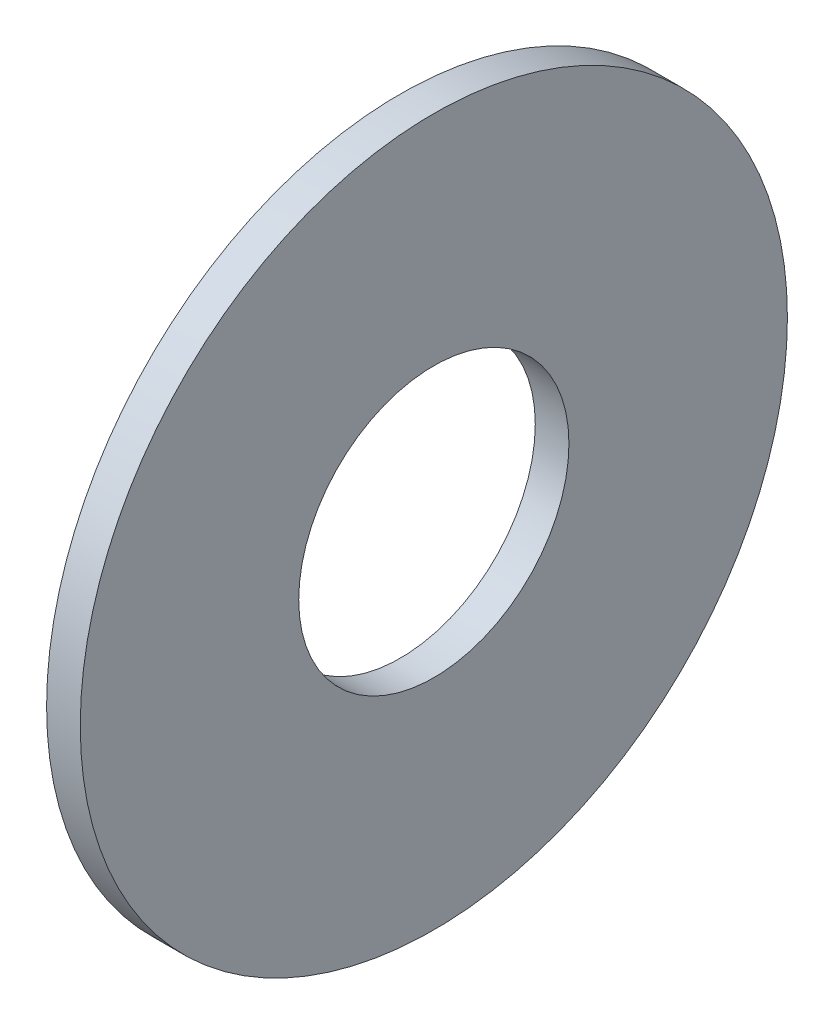
SolidWorks part; units mm, degrees
ref_plane "Front Plane" through (0, 0, 0) normal (0, 0, 1) x (1, 0, 0)
ref_plane "Top Plane" through (0, 0, 0) normal (0, 1, 0) x (1, 0, 0)
ref_plane "Right Plane" through (0, 0, 0) normal (1, 0, 0) x (0, 0, -1)
sketch "Sketch1" plane through (0, 0, 0) normal (1, 0, 0) x (0, 0, -1)
  circle A0 centre (0, 0) radius 10.5
  circle A1 centre (0, 0) radius 4 construction
  circle A2 centre (0, 0) radius 4.0125
  dimension "OD" = 21
  dimension "For Shaft Diameter" = 8
  dimension "ID" = 8.025
sketch "Sketch2" plane through (0, 0, 0) normal (0, 0, 1) x (1, 0, 0)
  line L0 (0.5, 0) -> (-0.5, 0) construction
  line L1 (0.5, -10.5) -> (-0.5, -10.5) construction
  line L2 (0.5, -10.5) -> (0.5, 10.5) construction
  line L3 (0.5, 10.5) -> (-0.5, 10.5) construction
  line L4 (-0.5, -10.5) -> (-0.5, 10.5) construction
  point P6 (0, 10.5)
  point P9 (0, -10.5)
  dimension "Thickness" = 1
sketch "Sketch3" plane through (0, 0, 0) normal (1, 0, 0) x (0, 0, -1)
  circle A1 centre (0, 0) radius 10.5 construction
  circle A3 centre (0, 0) radius 10.5
  circle A4 centre (0, 0) radius 4.0125 construction
  circle A5 centre (0, 0) radius 4.0125
extrude "Boss-Extrude1" add sketch "Sketch3" along normal up to vertex (0.5 mm away) and the other way up to vertex (0.5 mm away) up to point (0.5, 10.5, 0) other way up to point (-0.5, 10.5, 0)
